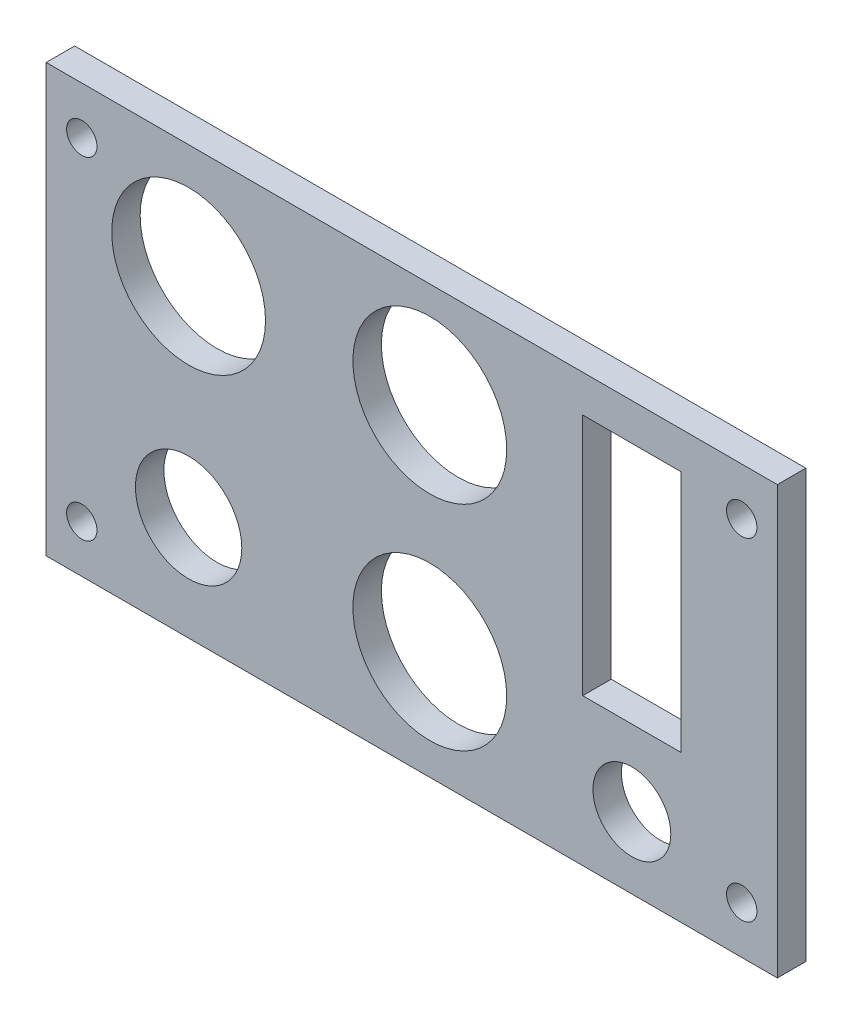
SolidWorks part; units mm, degrees
ref_plane "Alzado" through (0, 0, 0) normal (0, 0, 1) x (1, 0, 0)
ref_plane "Planta" through (0, 0, 0) normal (0, 1, 0) x (1, 0, 0)
ref_plane "Vista lateral" through (0, 0, 0) normal (1, 0, 0) x (0, 0, -1)
sketch "Croquis1" plane through (0, 0, 0) normal (0, 0, 1) x (1, 0, 0)
  line L1 (0, 0) -> (77, 0)
  line L2 (0, 0) -> (0, 45)
  line L3 (0, 45) -> (77, 45)
  line L4 (77, 0) -> (77, 45)
  dimension "D1" = 45
  dimension "D2" = 77
extrude "Saliente-Extruir1" add sketch "Croquis1" along normal blind 3
sketch "Croquis2" plane through (0, 0, 3) normal (0, 0, 1) x (1, 0, 0)
  line L0 (0, 45) -> (0, 0) construction
  line L1 (77, 45) -> (0, 45) construction
  line L2 (15, 33) -> (15, 11) construction
  line L3 (61.68, 15.5) -> (61.68, 7.5) construction
  line L4 (66.86, 41.1) -> (56.5, 41.1)
  line L5 (66.86, 41.1) -> (66.86, 15.5)
  line L6 (66.86, 15.5) -> (56.5, 15.5)
  line L7 (56.5, 41.1) -> (56.5, 15.5)
  line L8 (77, 0) -> (77, 45) construction
  line L9 (40.4, 0) -> (40.4, 45) construction
  line L10 (0, 0) -> (77, 0) construction
  line L11 (77, 22.5) -> (73.25, 22.5) construction
  line L12 (77, 0) -> (77, 45) construction
  line L13 (73.25, 22.5) -> (73.25, 40) construction
  line L14 (73.25, 40) -> (3.75, 40) construction
  line L15 (3.75, 40) -> (3.75, 5) construction
  line L16 (73.25, 5) -> (3.75, 5) construction
  line L17 (73.25, 5) -> (73.25, 22.5) construction
  line L18 (3.75, 22.5) -> (0, 22.5) construction
  circle A0 centre (15, 33) radius 8.1
  circle A1 centre (15, 11) radius 5.6
  circle A2 centre (61.68, 7.5) radius 4.1
  circle A3 centre (40.4, 33.95) radius 8.1
  circle A4 centre (40.4, 11.45) radius 8.1
  circle A5 centre (73.25, 40) radius 1.6
  circle A6 centre (73.25, 5) radius 1.6
  circle A7 centre (3.75, 5) radius 1.6
  circle A8 centre (3.75, 40) radius 1.6
  dimension "D1" = 16.2
  dimension "D4" = 11.2
  dimension "D6" = 8.2
  dimension "D17" = 3.2
  dimension "D2" = 15
  dimension "D3" = 12
  dimension "D5" = 22
  dimension "D7" = 8
  dimension "D8" = 3.9
  dimension "D9" = 29.5
  dimension "D10" = 10.14
  dimension "D11" = 20.5
  dimension "D12" = 11.05
  dimension "D13" = 36.6
  dimension "D14" = 22.5
  dimension "D15" = 35
  dimension "D16" = 69.5
extrude "Cortar-Extruir1" cut sketch "Croquis2" against normal up to next
